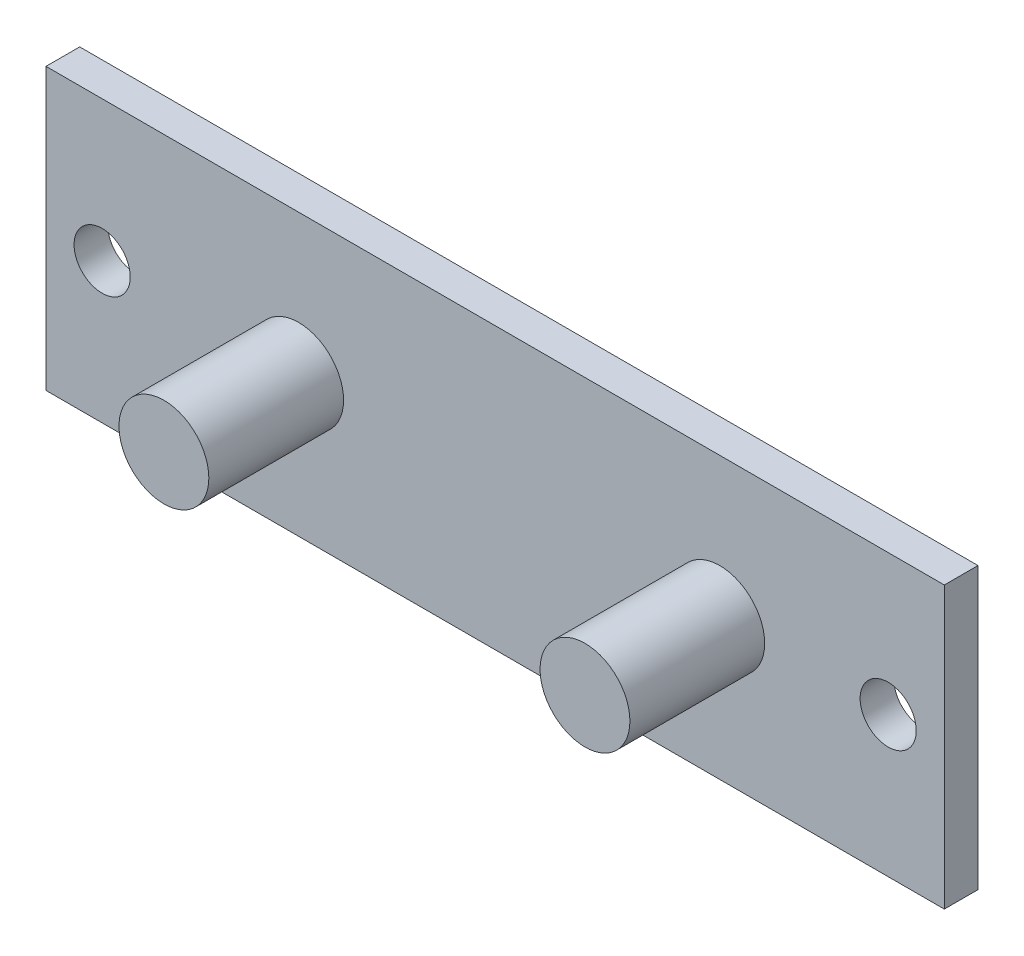
SolidWorks part; units mm, degrees
ref_plane "Ebene vorne" through (0, 0, 0) normal (0, 0, 1) x (1, 0, 0)
ref_plane "Ebene oben" through (0, 0, 0) normal (0, 1, 0) x (1, 0, 0)
ref_plane "Ebene rechts" through (0, 0, 0) normal (1, 0, 0) x (0, 0, -1)
sketch "Sketch1" plane through (0, 0, 0) normal (0, 0, 1) x (1, 0, 0)
  line L1 (0, 0) -> (-80, 0)
  line L2 (0, 0) -> (0, 25)
  line L3 (0, 25) -> (-80, 25)
  line L4 (-80, 0) -> (-80, 25)
  dimension "D4" = 80
  dimension "D5" = 25
extrude "Boss-Extrude1" add sketch "Sketch1" along normal blind 3
sketch "Sketch2" plane through (0, 0, 3) normal (0, 0, 1) x (1, 0, 0)
  line L0 (0, 0) -> (0, 25) construction
  line L1 (-80, 0) -> (0, 0) construction
  circle A0 centre (-57.5, 12.5) radius 4
  circle A1 centre (-20, 12.5) radius 4
  point P8 (-57.5, 10.161)
  point P9 (0, 0)
  dimension "D3" = 8
  dimension "D4" = 8
  dimension "D1" = 20
  dimension "D2" = 37.5
  dimension "D5" = 12.5
extrude "Boss-Extrude2" add sketch "Sketch2" along normal blind 12
sketch "Sketch3" plane through (0, 0, 3) normal (0, 0, 1) x (1, 0, 0)
  line L0 (-80, 25) -> (-80, 0) construction
  line L1 (-40, 25) -> (-40, 0) construction
  line L2 (0, 25) -> (-80, 25) construction
  line L3 (-80, 0) -> (0, 0) construction
  circle A0 centre (-75, 12.5) radius 2.5
  circle A2 centre (-5, 12.5) radius 2.5
  point P2 (0, 0)
  point P3 (-40, 12.5)
  dimension "D2" = 5
  dimension "D3" = 5
extrude "Cut-Extrude1" cut sketch "Sketch3" against normal blind 8
